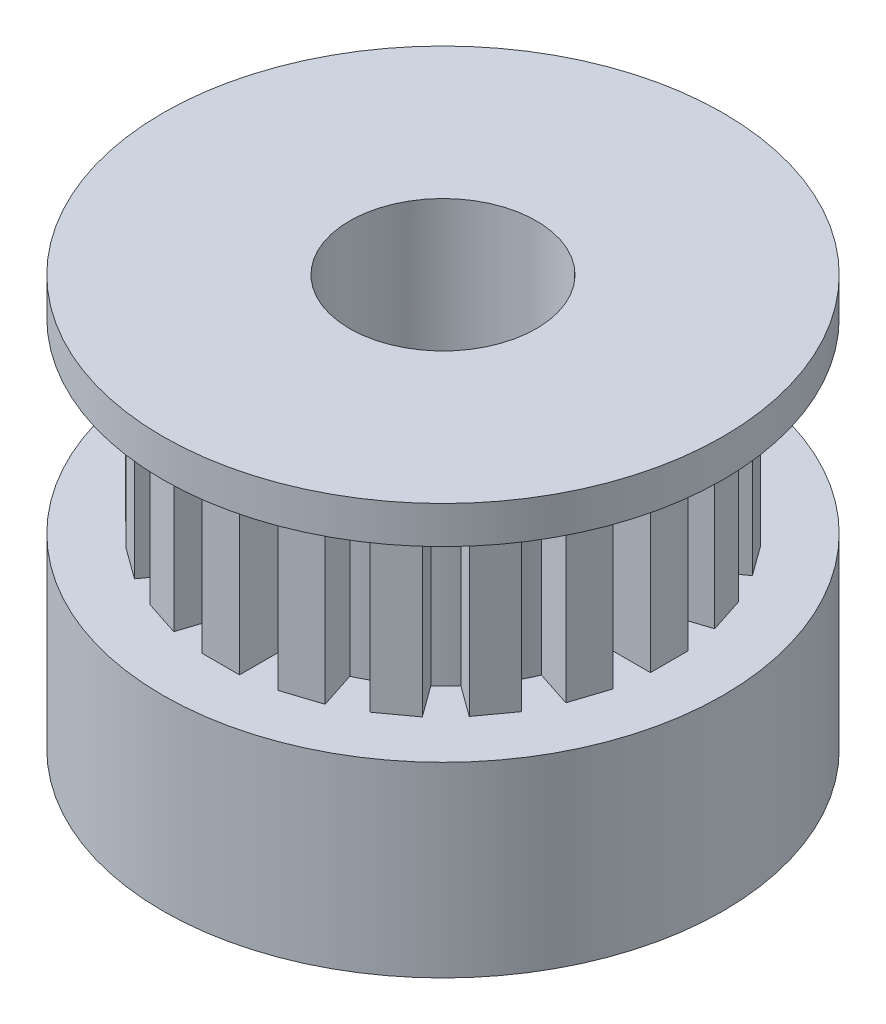
SolidWorks part; units mm, degrees
ref_plane "Ön Düzlem" through (0, 0, 0) normal (0, 0, 1) x (1, 0, 0)
ref_plane "Üst Düzlem" through (0, 0, 0) normal (0, 1, 0) x (1, 0, 0)
ref_plane "Sağ Düzlem" through (0, 0, 0) normal (1, 0, 0) x (0, 0, -1)
sketch "Çizim1" plane through (0, 0, 0) normal (0, 1, 0) x (1, 0, 0)
  circle A0 centre (0, 0) radius 7.5
extrude "Yükseklik-Ekstrüzyon1" add sketch "Çizim1" along normal blind 5
sketch "Çizim6" plane through (0, 5, 0) normal (0, 1, 0) x (1, 0, 0)
  circle A0 centre (0, 0) radius 5
extrude "Yükseklik-Ekstrüzyon5" add sketch "Çizim6" along normal blind 5
sketch "Çizim7" plane through (0, 10, 0) normal (0, 1, 0) x (1, 0, 0)
  line L0 (0, 5) -> (0, 6)
  line L1 (0, 6) -> (0.4468, 6)
  line L2 (0.4468, 6) -> (0.4468, 4.4288)
  line L3 (0.4468, 4.4288) -> (-0.5532, 4.4288)
  line L4 (-0.5532, 4.4288) -> (-0.5532, 6)
  line L5 (-0.5532, 6) -> (0, 6)
  circle A0 centre (0, 0) radius 5 construction
  circle A1 centre (0, 0) radius 5 construction
  circle M3 centre (0, 0) radius 5
extrude "Yükseklik-Ekstrüzyon6" add sketch "Çizim7" against normal blind 7 contours L2 L1 L0 M3 | L5 L4 L0 M3
pattern_circular "Dairesel Kaplama2" count 20 over 360 about axis through (0, 0, 0) along (0, 1, 0) of "Yükseklik-Ekstrüzyon6"
sketch "Çizim8" plane through (0, 10, 0) normal (0, 1, 0) x (1, 0, 0)
  circle A0 centre (0, 0) radius 7.5
extrude "Yükseklik-Ekstrüzyon7" add sketch "Çizim8" along normal blind 1
sketch "Çizim9" plane through (0, 11, 0) normal (0, 1, 0) x (1, 0, 0)
  circle A0 centre (0, 0) radius 2.5
extrude "Kes-Ekstrüzyon2" cut sketch "Çizim9" against normal blind 21
sketch "Çizim10" plane through (0, 0, 0) normal (1, 0, 0) x (0, 0, -1)
  circle A0 centre (0, 2.3612) radius 1.2
extrude "Kes-Ekstrüzyon3" cut sketch "Çizim10" against normal blind 21
